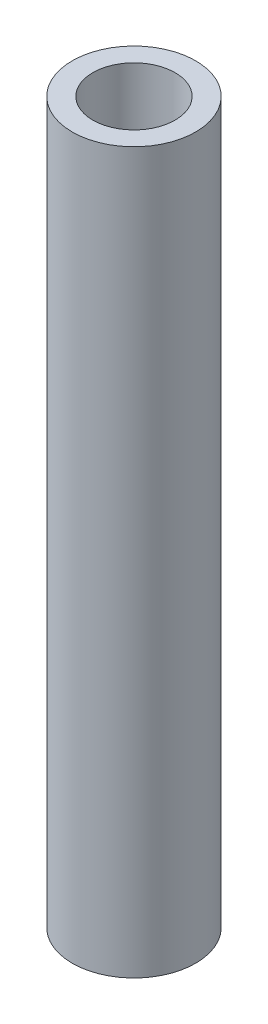
SolidWorks part; units mm, degrees
ref_plane "Front Plane" through (0, 0, 0) normal (0, 0, 1) x (1, 0, 0)
ref_plane "Top Plane" through (0, 0, 0) normal (0, 1, 0) x (1, 0, 0)
ref_plane "Right Plane" through (0, 0, 0) normal (1, 0, 0) x (0, 0, -1)
sketch "Sketch1" plane through (0, 0, 0) normal (0, 1, 0) x (1, 0, 0)
  circle A0 centre (0, 0) radius 3
  circle A1 centre (0, 0) radius 2
  dimension "D1" = 4
  dimension "D2" = 6
extrude "Boss-Extrude1" add sketch "Sketch1" along normal blind 35
